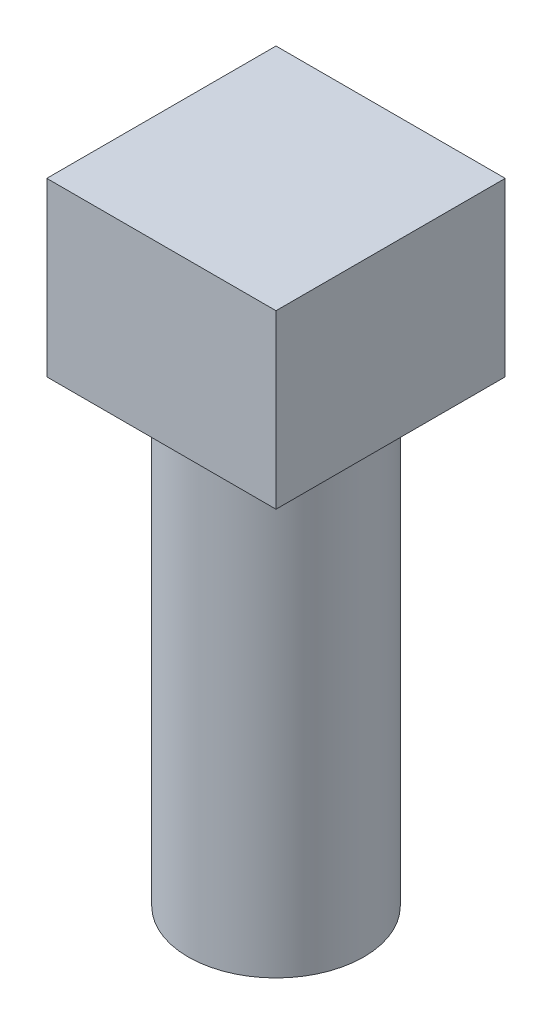
SolidWorks part; units mm, degrees
ref_plane "Front Plane" through (0, 0, 0) normal (0, 0, 1) x (1, 0, 0)
ref_plane "Top Plane" through (0, 0, 0) normal (0, 1, 0) x (1, 0, 0)
ref_plane "Right Plane" through (0, 0, 0) normal (1, 0, 0) x (0, 0, -1)
sketch "Sketch1" plane through (0, 0, 0) normal (0, 1, 0) x (1, 0, 0)
  circle A0 centre (0, 0) radius 5.842
extrude "Boss-Extrude1" add sketch "Sketch1" along normal blind 30.48
sketch "Sketch2" plane through (0, 30.48, 0) normal (0, 1, 0) x (1, 0, 0)
  line L1 (-7.62, -7.62) -> (7.62, -7.62)
  line L2 (-7.62, -7.62) -> (-7.62, 7.62)
  line L3 (-7.62, 7.62) -> (7.62, 7.62)
  line L4 (7.62, -7.62) -> (7.62, 7.62)
  line L5 (-7.62, -7.62) -> (7.62, 7.62) construction
  line L6 (-7.62, 7.62) -> (7.62, -7.62) construction
  point P0 (0, 0)
extrude "Boss-Extrude2" add sketch "Sketch2" along normal blind 11.43
